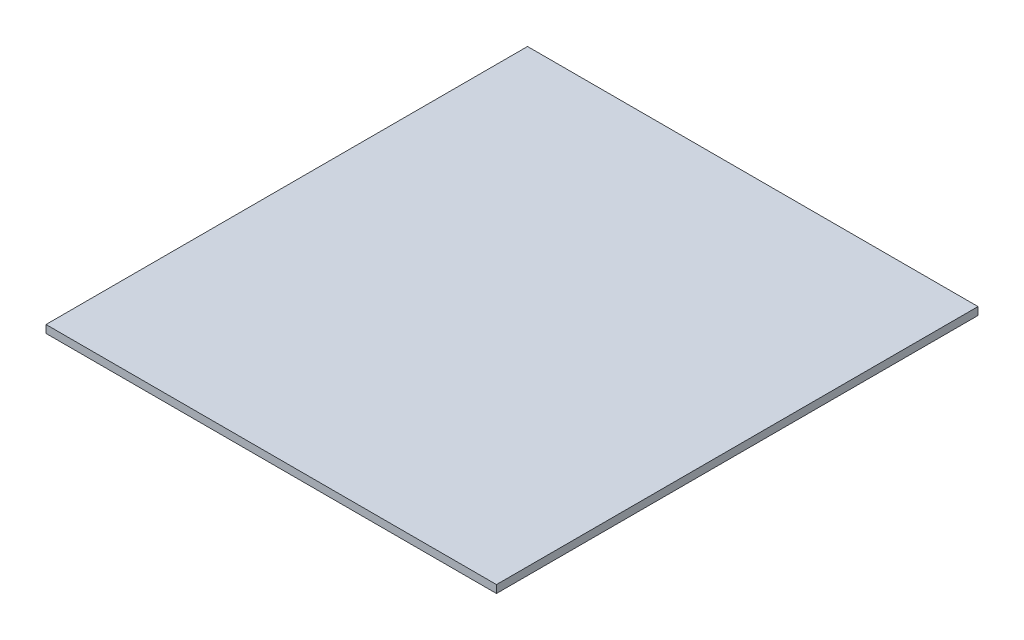
SolidWorks part; units mm, degrees
material "6061-T6 (SS)"
ref_plane "Front Plane" through (0, 0, 0) normal (0, 0, 1) x (1, 0, 0)
ref_plane "Top Plane" through (0, 0, 0) normal (0, 1, 0) x (1, 0, 0)
ref_plane "Right Plane" through (0, 0, 0) normal (1, 0, 0) x (0, 0, -1)
sketch "Sketch1" plane through (0, 0, 0) normal (0, 1, 0) x (1, 0, 0)
  line L1 (184.15, -196.85) -> (-184.15, -196.85)
  line L2 (184.15, -196.85) -> (184.15, 196.85)
  line L3 (184.15, 196.85) -> (-184.15, 196.85)
  line L4 (-184.15, -196.85) -> (-184.15, 196.85)
  line L5 (184.15, -196.85) -> (-184.15, 196.85) construction
  line L6 (184.15, 196.85) -> (-184.15, -196.85) construction
  point P0 (0, 0)
  dimension "D1" = 393.7
  dimension "D2" = 368.3
extrude "Boss-Extrude1" add sketch "Sketch1" along normal blind 6.35
